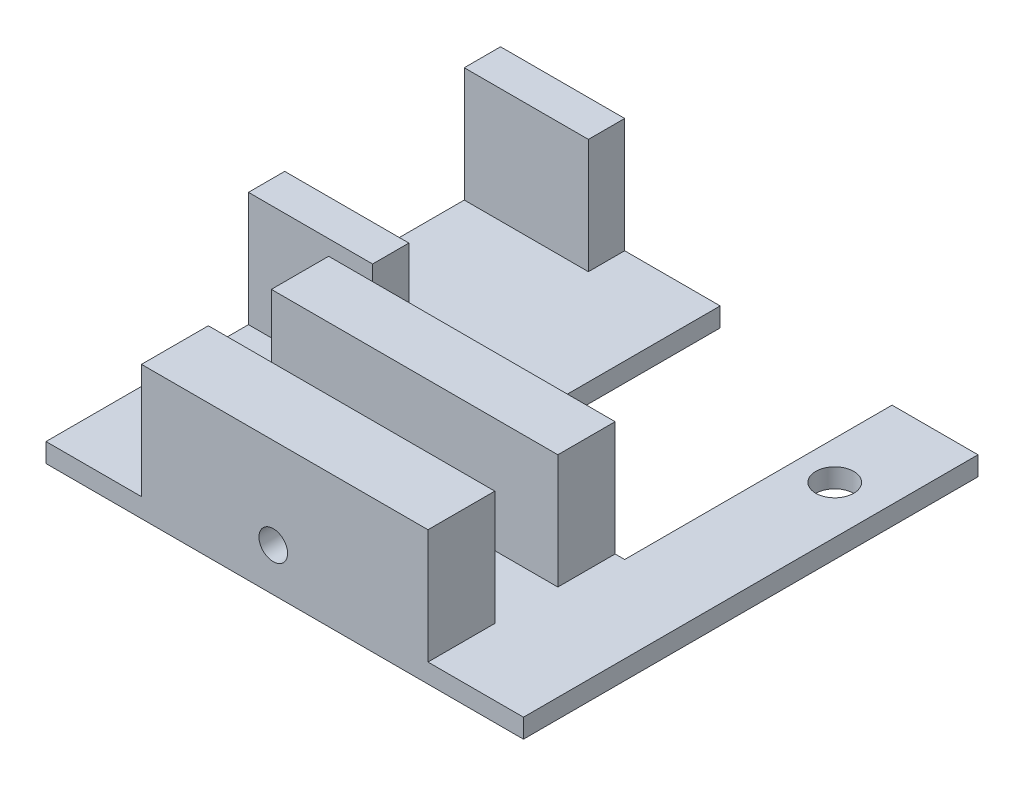
SolidWorks part; units mm, degrees
ref_plane "Front Plane" through (0, 0, 0) normal (0, 0, 1) x (1, 0, 0)
ref_plane "Top Plane" through (0, 0, 0) normal (0, 1, 0) x (1, 0, 0)
ref_plane "Right Plane" through (0, 0, 0) normal (1, 0, 0) x (0, 0, -1)
sketch "Sketch1" plane through (0, 0, 0) normal (0, 1, 0) x (1, 0, 0)
  line L1 (-31.75, -30.226) -> (31.75, -30.226)
  line L2 (-31.75, -30.226) -> (-31.75, 30.226)
  line L3 (-31.75, 30.226) -> (31.75, 30.226)
  line L4 (31.75, -30.226) -> (31.75, 30.226)
  line L5 (-31.75, -30.226) -> (31.75, 30.226) construction
  line L6 (-31.75, 30.226) -> (31.75, -30.226) construction
  point P0 (0, 0)
  dimension "D1" = 60.452
  dimension "D2" = 63.5
extrude "Boss-Extrude1" add sketch "Sketch1" along normal mid plane 2.54
sketch "Sketch2" plane through (0, 1.27, 0) normal (0, 1, 0) x (1, 0, 0)
  line L0 (-31.75, 30.226) -> (-31.75, -30.226) construction
  line L1 (-31.75, 30.226) -> (-15.24, 30.226)
  line L2 (-31.75, 30.226) -> (-31.75, 25.4)
  line L3 (-31.75, 25.4) -> (-15.24, 25.4)
  line L4 (-15.24, 30.226) -> (-15.24, 25.4)
  line L5 (-31.75, 1.524) -> (-15.24, 1.524)
  line L6 (-31.75, 1.524) -> (-31.75, -3.302)
  line L7 (-31.75, -3.302) -> (-15.24, -3.302)
  line L8 (-15.24, 1.524) -> (-15.24, -3.302)
  line L10 (-19.05, -30.226) -> (19.05, -30.226)
  line L11 (-19.05, -30.226) -> (-19.05, -21.336)
  line L12 (-19.05, -21.336) -> (19.05, -21.336)
  line L13 (19.05, -30.226) -> (19.05, -21.336)
  line L14 (-19.05, -12.954) -> (19.05, -12.954)
  line L15 (-19.05, -12.954) -> (-19.05, -5.334)
  line L16 (-19.05, -5.334) -> (19.05, -5.334)
  line L17 (19.05, -12.954) -> (19.05, -5.334)
  dimension "D1" = 4.826
  dimension "D2" = 4.826
  dimension "D3" = 23.876
  dimension "D4" = 16.51
  dimension "D5" = 2.032
  dimension "D6" = 7.62
  dimension "D7" = 8.89
  dimension "D8" = 38.1
  dimension "D9" = 12.7
extrude "Boss-Extrude2" add sketch "Sketch2" along normal blind 15.24
sketch "Sketch3" plane through (0, 0, 5.334) normal (0, 0, -1) x (-1, 0, 0)
  line L0 (-19.05, 16.51) -> (-19.05, 1.27) construction
  line L1 (-19.05, 1.27) -> (19.05, 1.27) construction
  circle A0 centre (1.524, 4.445) radius 1.905
  dimension "D1" = 3.81
  dimension "D2" = 20.574
  dimension "D3" = 3.175
extrude "Cut-Extrude1" cut sketch "Sketch3" against normal through all
sketch "Sketch4" plane through (0, 0, 5.334) normal (0, 0, -1) x (-1, 0, 0)
  circle A0 centre (1.524, 4.445) radius 3.175
extrude "Cut-Extrude2" cut sketch "Sketch4" against normal up to surface (7.62 mm away) up to face at (-3.429, 4.445, 12.954)
sketch "Sketch5" plane through (0, -1.27, 0) normal (0, -1, 0) x (1, 0, 0)
  line L0 (20.32, -29.1207) -> (20.32, -4.8687) construction
  line L1 (-2.54, -4.8687) -> (20.32, -4.8687) construction
  line L2 (-2.54, -29.1207) -> (-2.54, -4.8687) construction
  line L3 (20.32, -29.1207) -> (20.32, -4.8687)
  line L4 (-2.54, -4.8687) -> (20.32, -4.8687)
  line L5 (-2.54, -29.1207) -> (-2.54, -4.8687)
  line L6 (31.75, -30.226) -> (-31.75, -30.226) construction
  line L7 (-2.54, -29.1207) -> (20.32, -29.1207)
  line L8 (-2.54, -29.1207) -> (-2.54, -30.226)
  line L9 (-2.54, -30.226) -> (20.32, -30.226)
  line L10 (20.32, -29.1207) -> (20.32, -30.226)
  line L11 (19.05, 5.334) -> (-1.524, 5.334) construction
  line L12 (20.32, -4.8687) -> (-2.54, -4.8687)
  line L13 (20.32, -4.8687) -> (20.32, 5.334)
  line L14 (20.32, 5.334) -> (-2.54, 5.334)
  line L15 (-2.54, -4.8687) -> (-2.54, 5.334)
  line L17 (20.32, 5.334) -> (31.75, 5.334)
  line L18 (20.32, 5.334) -> (20.32, -30.226)
  line L19 (20.32, -30.226) -> (31.75, -30.226)
  line L20 (31.75, 5.334) -> (31.75, -30.226)
  line M1 (31.75, -30.226) -> (31.75, 30.226)
  line M4 (-31.75, -30.226) -> (31.75, -30.226)
extrude "Cut-Extrude3" cut sketch "Sketch5" against normal through all contours L5 L7 L4 M1 | L7 L8 M4 M1 | L15 L4 L14 M1
sketch "Sketch6" plane through (0, 1.27, 0) normal (0, 1, 0) x (1, 0, 0)
  line L0 (-19.05, -12.954) -> (19.05, -12.954) construction
  line L1 (-31.75, -3.302) -> (-31.75, -30.226) construction
  line L2 (31.75, -30.226) -> (31.75, 30.226) construction
  line L3 (19.05, -5.334) -> (-19.05, -5.334) construction
  line L4 (-2.54, 30.226) -> (-2.54, -5.334) construction
  line L7 (31.75, 30.226) -> (20.32, 30.226) construction
  circle A0 centre (-19.05, -17.399) radius 2.54
  circle A1 centre (25.4, 17.526) radius 2.54
  circle A2 centre (-6.35, -1.524) radius 2.54
  dimension "D4" = 5.08
  dimension "D5" = 5.08
  dimension "D6" = 5.08
  dimension "D1" = 4.445
  dimension "D2" = 12.7
  dimension "D3" = 6.35
  dimension "D7" = 3.81
  dimension "D8" = 3.81
  dimension "D9" = 12.7
hole_wizard "#8 (0.199) Diameter Hole1" positions "3DSketch1" profile "Sketch7" hole size "#8" standard "ANSI Inch" end condition through all
sketch3d "3DSketch1"
  point P0 (-6.35, 1.27, 1.524)
  point P3 (-19.05, 1.27, 17.399)
  point P6 (25.4, 1.27, -17.526)
sketch "Sketch7" plane through (-6.35, 1.27, 1.524) normal (1, 0, 0) x (0, 0, 1)
  line L0 (0, 0) -> (0, 2.54)
  line L1 (0, 2.54) -> (2.5273, 2.54)
  line L2 (2.5273, 2.54) -> (2.5273, 0)
  line L5 (2.5273, 0) -> (0, 0)
  line L11 (0, -6.35) -> (0, 107.95) construction
  dimension "Thru Hole Dia." = 5.0546
  dimension "Thru Hole Depth" = 2.54
